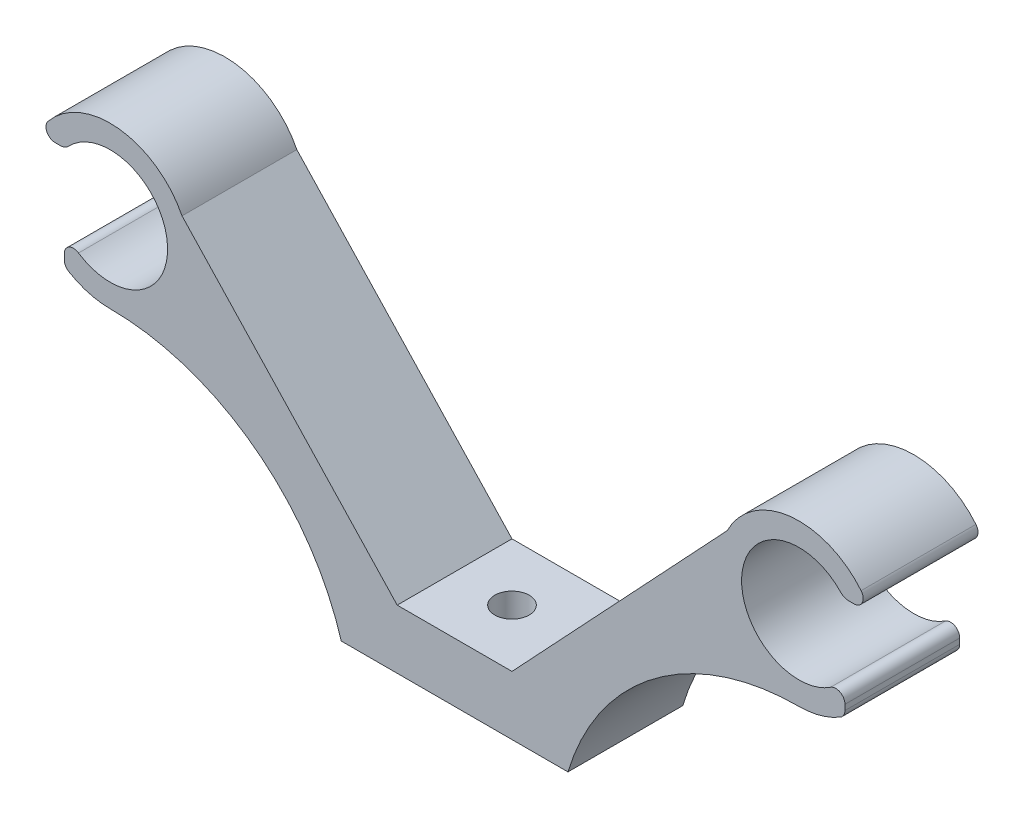
SolidWorks part; units mm, degrees
ref_plane "Front Plane" through (0, 0, 0) normal (0, 0, 1) x (1, 0, 0)
ref_plane "Top Plane" through (0, 0, 0) normal (0, 1, 0) x (1, 0, 0)
ref_plane "Right Plane" through (0, 0, 0) normal (1, 0, 0) x (0, 0, -1)
sketch "Sketch1" plane through (0, 0, 0) normal (0, 0, 1) x (1, 0, 0)
  line L0 (9.8754, 0) -> (-9.8754, 0)
  line L1 (5, 5.1454) -> (-5, 5.1454)
  line L3 (-5, 5.1454) -> (-23.741, 25.1346)
  line L4 (34.348, 25.1346) -> (34.7916, 25.1346)
  line L5 (-34, 16.6896) -> (-34, 17.1626)
  line L6 (-34.348, 25.1346) -> (-34.7916, 25.1346)
  line L7 (34, 16.6896) -> (34, 17.1626)
  line L8 (5, 5.1454) -> (23.741, 25.1346)
  arc A0 (-32.7586, 17.8299) -> (-33.6234, 25.4455) centre (-30, 22) ccw
  arc A1 (-9.8754, 0) -> (-30, 15) centre (-30, -6) ccw
  arc A2 (-33.6129, 16.0044) -> (-30, 15) centre (-30, 22) ccw
  arc A3 (-23.741, 25.1346) -> (-35.4099, 26.4422) centre (-30, 22) ccw
  arc A4 (-34.348, 25.1346) -> (-33.6234, 25.4455) centre (-34.348, 26.1346) ccw
  arc A5 (-34.7916, 25.1346) -> (-35.4099, 26.4422) centre (-34.7916, 25.9346) cw
  arc A6 (-34, 16.6896) -> (-33.6129, 16.0044) centre (-33.2, 16.6896) ccw
  arc A7 (-34, 17.1626) -> (-32.7586, 17.8299) centre (-33.2, 17.1626) cw
  arc A8 (34, 17.1626) -> (32.7586, 17.8299) centre (33.2, 17.1626) ccw
  arc A9 (34, 16.6896) -> (33.6129, 16.0044) centre (33.2, 16.6896) cw
  arc A10 (34.7916, 25.1346) -> (35.4099, 26.4422) centre (34.7916, 25.9346) ccw
  arc A11 (34.348, 25.1346) -> (33.6234, 25.4455) centre (34.348, 26.1346) cw
  arc A12 (23.741, 25.1346) -> (35.4099, 26.4422) centre (30, 22) cw
  arc A13 (33.6129, 16.0044) -> (30, 15) centre (30, 22) cw
  arc A14 (9.8754, 0) -> (30, 15) centre (30, -6) cw
  arc A15 (32.7586, 17.8299) -> (33.6234, 25.4455) centre (30, 22) cw
  dimension "D4" = 4
  dimension "D5" = 1
  dimension "D6" = 0.8
  dimension "D7" = 0.8
extrude "Boss-Extrude1" add sketch "Sketch1" along normal blind 10
sketch "Sketch2" plane through (0, 5.1454, 0) normal (0, 1, 0) x (1, 0, 0)
  line L1 (5, 0) -> (-5, 0) construction
  circle A0 centre (0, -5) radius 1.5
  dimension "D1" = 5
extrude "Cut-Extrude1" cut sketch "Sketch2" against normal blind 10
